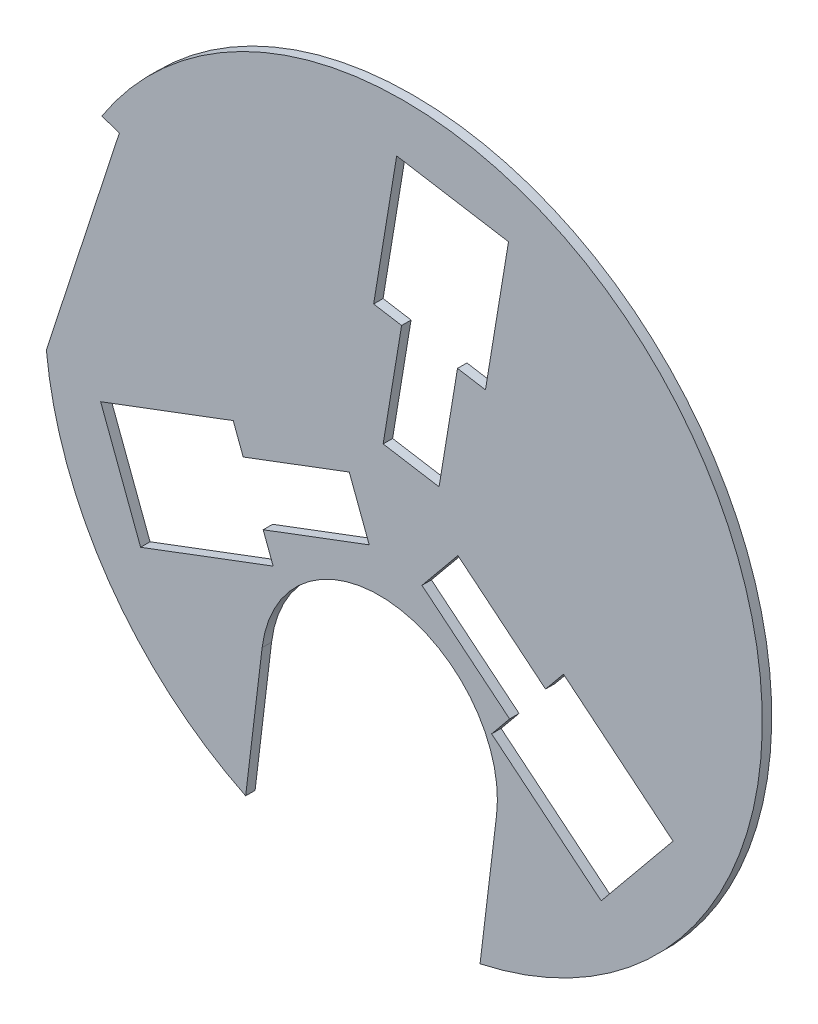
SolidWorks part; units mm, degrees
ref_plane "Front Plane" through (0, 0, 0) normal (0, 0, 1) x (1, 0, 0)
ref_plane "Top Plane" through (0, 0, 0) normal (0, 1, 0) x (1, 0, 0)
ref_plane "Right Plane" through (0, 0, 0) normal (1, 0, 0) x (0, 0, -1)
sketch "Sketch1" plane through (0, 0, 0) normal (0, 0, 1) x (1, 0, 0)
  line L0 (-33.6269, -46.6739) -> (85.7894, 6.2456) construction
  line L1 (45.0418, -148.5359) -> (136.4333, -108.0356) construction
  line L2 (-83.5307, -170.6535) -> (-74.8066, -98.3048)
  line L3 (40.5703, -185.618) -> (49.2944, -113.2693)
  line L4 (44.3451, -154.3136) -> (144.1554, -110.0825) construction
  line L5 (-159.7043, 102.9298) -> (105.4883, 16.6584) construction
  line L7 (-189.0505, -18.9715) -> (141.7031, -126.571) construction
  line L8 (78.0643, -133.9019) -> (80.09, -138.4732) construction
  line L9 (111.1114, -50.895) -> (164.8514, -82.8051) construction
  line L10 (45.0418, -148.5359) -> (79.7833, -133.1401) construction
  line L11 (45.0418, -148.5359) -> (59.2221, -180.5346) construction
  line L12 (59.2221, -180.5346) -> (93.9636, -165.1388) construction
  line L13 (79.7833, -133.1401) -> (93.9636, -165.1388) construction
  line L14 (-74.2573, -43.9983) -> (-68.9701, -58.0356)
  line L15 (-160.3054, -28.3227) -> (-90.119, -1.8865)
  line L16 (-160.3054, -28.3227) -> (-139.1564, -84.4718)
  line L17 (-139.1564, -84.4718) -> (-68.9701, -58.0356)
  line L18 (-90.119, -1.8865) -> (-84.8318, -15.9238)
  line L19 (-84.8318, -15.9238) -> (-28.6827, 5.2252)
  line L20 (-74.2573, -43.9983) -> (-18.1082, -22.8493)
  line L21 (-28.6827, 5.2252) -> (-18.1082, -22.8493)
  line L22 (-149.7309, -56.3973) -> (-23.3955, -8.8121) construction
  line L23 (-0.975, 86.3079) -> (-15.7753, 88.7476)
  line L24 (55.6245, 152.9899) -> (43.4258, 78.9886)
  line L25 (55.6245, 152.9899) -> (-3.5765, 162.7489)
  line L26 (-3.5765, 162.7489) -> (-15.7753, 88.7476)
  line L27 (43.4258, 78.9886) -> (28.6255, 81.4284)
  line L28 (28.6255, 81.4284) -> (18.8665, 22.2273)
  line L29 (-0.975, 86.3079) -> (-10.734, 27.1068)
  line L30 (18.8665, 22.2273) -> (-10.734, 27.1068)
  line L31 (26.024, 157.8694) -> (4.0663, 24.6671) construction
  line L32 (75.2323, -42.3096) -> (84.7453, -30.712)
  line L33 (104.6809, -124.6672) -> (46.6933, -77.1021)
  line L34 (104.6809, -124.6672) -> (142.7329, -78.2771)
  line L35 (142.7329, -78.2771) -> (84.7453, -30.712)
  line L36 (46.6933, -77.1021) -> (56.2063, -65.5046)
  line L37 (56.2063, -65.5046) -> (9.8162, -27.4525)
  line L38 (75.2323, -42.3096) -> (28.8422, -4.2575)
  line L39 (9.8162, -27.4525) -> (28.8422, -4.2575)
  line L40 (123.7069, -101.4722) -> (19.3292, -15.855) construction
  line L41 (19.3292, -15.855) -> (0, 0) construction
  line L42 (4.0663, 24.6671) -> (0, 0) construction
  line L43 (0, 0) -> (-23.3955, -8.8121) construction
  line L44 (-189.0505, -18.9715) -> (-150.3807, 99.8967)
  line L45 (-150.3807, 99.8967) -> (-159.7043, 102.9298)
  line L46 (-33.6269, -46.6739) -> (-35.6526, -42.1026) construction
  line L47 (-35.6526, -42.1026) -> (89.46, 13.3412) construction
  arc A0 (40.5703, -185.618) -> (-159.7043, 102.9298) centre (0, 0) ccw
  arc A1 (49.2944, -113.2693) -> (-74.8066, -98.3048) centre (-12.7561, -105.787) ccw
  circle A2 centre (111.1114, -50.895) radius 62.5 construction
  arc A3 (89.46, 13.3412) -> (144.1554, -110.0825) centre (111.1114, -50.895) cw construction
  arc A4 (-189.0505, -18.9715) -> (-83.5307, -170.6535) centre (0, 0) ccw
  point P12 (0, 0)
  point P59 (-151.0217, 115.2929)
  point P60 (0, 0)
  point P61 (0, 0)
  point P63 (-165.955, 92.6976)
  dimension "D1" = 125
  dimension "D8" = 62.5
  dimension "D23" = 190
  dimension "D2" = 125
  dimension "D3" = 25
  dimension "D5" = 5
  dimension "D6" = 38
  dimension "D7" = 35
  dimension "D9" = 75
  dimension "D10" = 60
  dimension "D11" = 30
  dimension "D12" = 60
  dimension "D13" = 75
  dimension "D14" = 60
  dimension "D15" = 30
  dimension "D16" = 60
  dimension "D17" = 75
  dimension "D18" = 60
  dimension "D19" = 30
  dimension "D20" = 60
  dimension "D21" = 120
  dimension "D22" = 120
  dimension "D24" = 5
extrude "Boss-Extrude1" add sketch "Sketch1" along normal blind 5
